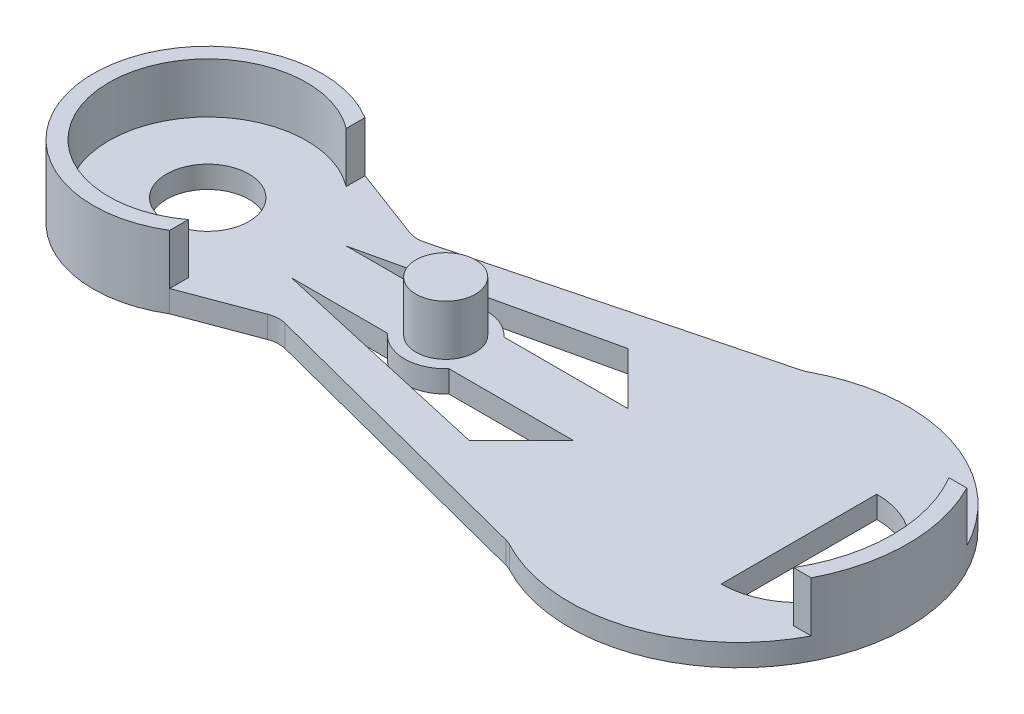
SolidWorks part; units mm, degrees
ref_plane "Front Plane" through (0, 0, 0) normal (0, 0, 1) x (1, 0, 0)
ref_plane "Top Plane" through (0, 0, 0) normal (0, 1, 0) x (1, 0, 0)
ref_plane "Right Plane" through (0, 0, 0) normal (1, 0, 0) x (0, 0, -1)
sketch "Sketch1" plane through (0, 0, 0) normal (0, 1, 0) x (1, 0, 0)
  line L0 (0, 0) -> (-126.4909, 0)
  line L1 (-48.3712, -10.6702) -> (-39.6996, -7.4178)
  line L4 (-48.3712, 10.6702) -> (-39.6996, 7.4178)
  line L5 (-42.7478, -3) -> (-32.2365, -3)
  line L6 (-11.9505, 8.5) -> (9.7173, 8.5)
  line L7 (-11.9505, 8.5) -> (-11.9505, -8.5)
  line L8 (-11.9505, -8.5) -> (9.7173, -8.5)
  line L9 (9.7173, 8.5) -> (9.7173, -8.5)
  line L10 (-11.9505, 8.5) -> (9.7173, -8.5) construction
  line L11 (-11.9505, -8.5) -> (9.7173, 8.5) construction
  line L12 (-25.5283, -3) -> (-11.9505, -3)
  line L13 (-25.5283, 3) -> (-11.9505, 3)
  line L14 (-42.7478, 3) -> (-32.2365, 3)
  line L15 (-11.9505, -3) -> (-17.6349, -8.6844)
  line L16 (-17.6349, -8.6844) -> (-42.7478, -3)
  line L17 (-11.9505, 3) -> (-17.6349, 8.6844)
  line L18 (-17.6349, 8.6844) -> (-42.7478, 3)
  line L19 (-39.6996, 7.4178) -> (-5.8577, 16.1769)
  line L20 (-39.6996, -7.4178) -> (-5.8577, -16.1769)
  arc A0 (12.0105, -16.2224) -> (12.0105, 16.2224) centre (3.1176, 0) ccw
  circle A1 centre (-54.8824, 0) radius 12.5
  circle A2 centre (-54.8824, 0) radius 4.5
  arc A3 (-32.2365, -3) -> (-25.5283, -3) centre (-28.8824, 0) ccw
  arc A4 (-25.5283, 3) -> (-32.2365, 3) centre (-28.8824, 0) ccw
  arc A5 (9.7173, -8.5) -> (9.7173, 8.5) centre (9.7173, 0) ccw
  arc A8 (-5.8577, -16.1769) -> (-5.8577, 16.1769) centre (3.1176, 0) ccw
  point P8 (-1.1166, 0)
  dimension "D1" = 58
  dimension "D2" = 37
  dimension "D3" = 25
  dimension "D4" = 9
  dimension "D6" = 9
  dimension "D5" = 26
  dimension "D7" = 17
  dimension "D8" = 3
  dimension "D9" = 3
extrude "Boss-Extrude1" add sketch "Sketch1" along normal blind 2.4
fillet "Fillet1" radius 3 4 edges at (-39.6996, 1.2, -7.4178) (-39.6996, 1.2, 7.4178) (-5.8577, 1.2, -16.1769) (-5.8577, 1.2, 16.1769)
sketch "Sketch2" plane through (0, 2.4, 0) normal (0, 1, 0) x (1, 0, 0)
  line L1 (17.6086, 8.5) -> (19.5493, 8.5)
  line L2 (17.6086, -8.5) -> (19.5493, -8.5)
  line L3 (-48.3712, 10.6702) -> (-48.3712, -10.6702)
  circle A0 centre (-54.8824, 0) radius 2.15
  arc A1 (-48.3712, 10.6702) -> (-48.3712, -10.6702) centre (-54.8824, 0) ccw
  arc A2 (-48.3712, 8.6212) -> (-48.3712, -8.6212) centre (-54.8824, 0) ccw
  arc A7 (-48.3712, 10.6702) -> (-48.3712, -10.6702) centre (-54.8824, 0) ccw construction
  circle A8 centre (19.3137, -8.9884) radius 0.0231
  circle A9 centre (-3.8884, 17.1139) radius 0.0075
  arc A10 (3.1176, 18.5) -> (3.1176, -18.5) centre (3.1176, 0) cw
  arc A11 (-5.5582, -16.3395) -> (-5.5582, 16.3395) centre (3.1176, 0) ccw construction
  arc A12 (17.6086, 8.5) -> (17.6086, -8.5) centre (3.1176, 0) cw
  arc A13 (3.1176, 16.8) -> (3.1176, -16.8) centre (3.1176, 0) cw construction
  circle A14 centre (-28.8824, 0) radius 4.5
  circle A15 centre (-28.8824, 0) radius 3.25
  arc M16 (-48.3712, 10.6702) -> (-48.3712, -10.6702) centre (-54.8824, 0) ccw
  arc M21 (-5.5582, -16.3395) -> (-5.5582, 16.3395) centre (3.1176, 0) ccw
  dimension "D1" = 1.6962
  dimension "D3" = 9
  dimension "D4" = 6.5
  dimension "D2" = 1.7
extrude "Boss-Extrude2" add sketch "Sketch2" along normal blind 5.5 contours A15 | A2 L3 M16 | L1 A12 L2 M21 | A14
